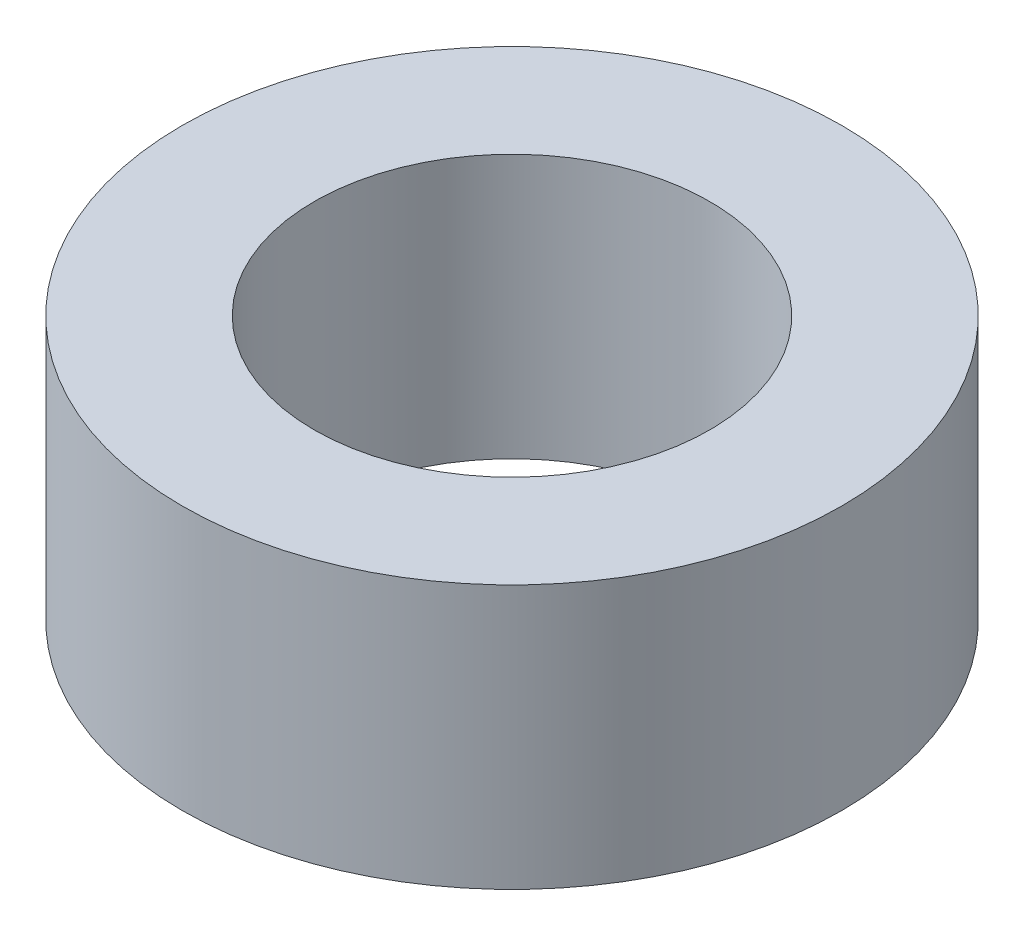
SolidWorks part; units mm, degrees
material "Nylon 101"
ref_plane "Front Plane" through (0, 0, 0) normal (0, 0, 1) x (1, 0, 0)
ref_plane "Top Plane" through (0, 0, 0) normal (0, 1, 0) x (1, 0, 0)
ref_plane "Right Plane" through (0, 0, 0) normal (1, 0, 0) x (0, 0, -1)
sketch "Sketch1" plane through (0, 0, 0) normal (0, 1, 0) x (1, 0, 0)
  circle A0 centre (0, 0) radius 7.9375
extrude "Boss-Extrude1" add sketch "Sketch1" along normal blind 6.35
sketch "Sketch2" plane through (0, 6.35, 0) normal (0, 1, 0) x (1, 0, 0)
  circle A0 centre (0, 0) radius 4.7625
extrude "Cut-Extrude1" cut sketch "Sketch2" against normal through all
